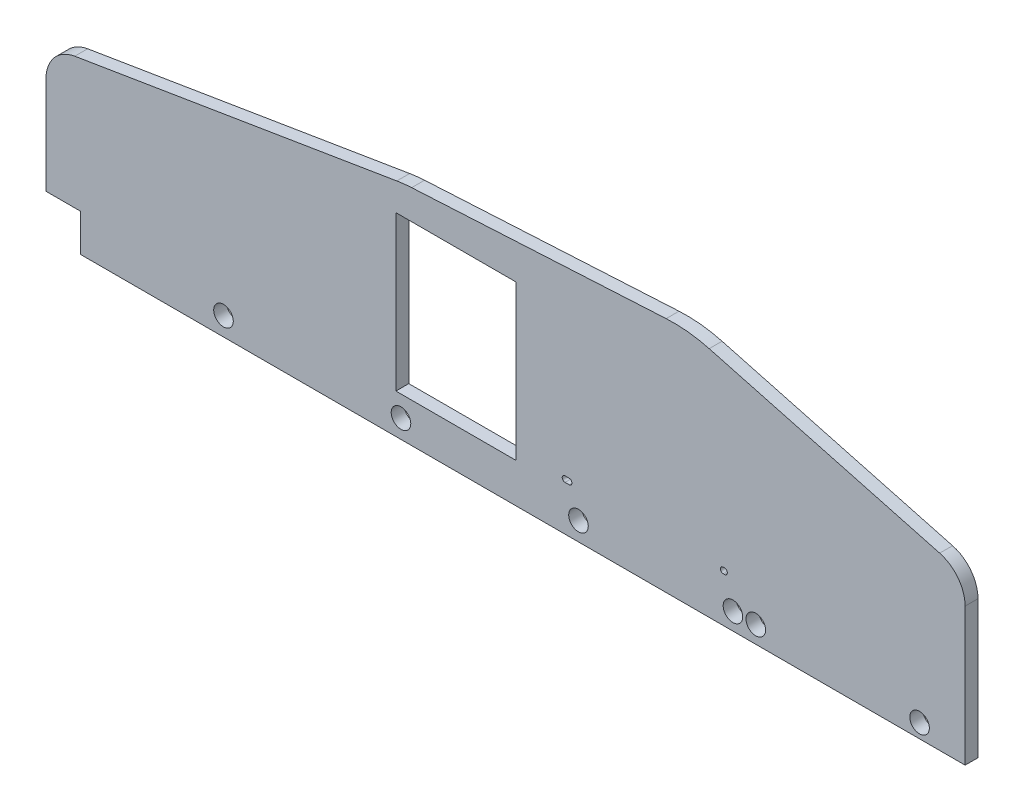
SolidWorks part; units mm, degrees
material "PC High Viscosity"
ref_plane "Front Plane" through (0, 0, 0) normal (0, 0, 1) x (1, 0, 0)
ref_plane "Top Plane" through (0, 0, 0) normal (0, 1, 0) x (1, 0, 0)
ref_plane "Right Plane" through (0, 0, 0) normal (1, 0, 0) x (0, 0, -1)
sketch "Sketch2" plane through (0, 0, 0) normal (0, 0, 1) x (1, 0, 0)
  line L0 (-340, 26.4) -> (-340, 121.4)
  line L1 (135, 176.4) -> (-75, 165)
  line L2 (135, 176.4) -> (340, 121.4)
  line L3 (340, 121.4) -> (340, 26.4)
  line L4 (340, 26.4) -> (340, 0)
  line L5 (-75, 165) -> (-340, 121.4)
  line L6 (340, 0) -> (-340, 0)
  line L7 (-340, 0) -> (-340, 26.4)
  circle A0 centre (-208.682, 13.7) radius 7.239
  circle A1 centre (-77.364, 13.7) radius 7.239
  circle A2 centre (53.954, 13.7) radius 7.239
  circle A3 centre (185.1267, 12.7) radius 7.239
  circle A4 centre (306.2847, 10.414) radius 7.239
  circle A5 centre (168.2251, 12.7) radius 7.239
  dimension "D7" = 14.478
  dimension "D11" = 12.7
  dimension "D1" = 165
  dimension "D2" = 680
  dimension "D3" = 95
  dimension "D4" = 475
  dimension "D5" = 150
  dimension "D6" = 210
  dimension "D8" = 95
  dimension "D9" = 26.4
  dimension "D12" = 10.414
extrude "Boss-Extrude1" add sketch "Sketch2" along normal mid plane 9.525
fillet "Fillet1" radius 25.4 2 edges at (340, 121.4, 0) (-340, 121.4, 0)
fillet "Fillet2" radius 101.6 2 edges at (-75, 165, 0) (135, 176.4, 0)
sketch "Sketch3" plane through (0, 0, 4.7625) normal (0, 0, 1) x (1, 0, 0)
  line L0 (0, 0) -> (0, 192.0016) construction
  line L1 (-340, 0) -> (-314.6, 0)
  line L2 (-340, 0) -> (-340, 27.686)
  line L3 (-340, 27.686) -> (-314.6, 27.686)
  line L4 (-314.6, 0) -> (-314.6, 27.686)
  line L5 (0, 192.0016) -> (0, -60.0751) construction
  dimension "D1" = 25.4
  dimension "D2" = 27.686
extrude "Cut-Extrude1" cut sketch "Sketch3" against normal through all
sketch "Sketch5" plane through (0, 0, 4.7625) normal (0, 0, 1) x (1, 0, 0)
  line L1 (-314.6, 0) -> (340, 0) construction
  line L3 (-81.1185, 29.1465) -> (7.7815, 29.1465)
  line L5 (7.7815, 29.1465) -> (7.7815, 143.4465)
  line L6 (7.7815, 143.4465) -> (-81.1185, 143.4465)
  line L7 (340, 0) -> (340, 101.9164) construction
  line L8 (-81.1185, 29.1465) -> (-81.1185, 143.4465)
  dimension "D2" = 29.1465
  dimension "D1" = 332.2185
  dimension "D3" = 114.3
  dimension "D4" = 88.9
extrude "Cut-Extrude2" cut sketch "Sketch5" against normal through all
sketch "Sketch8" plane through (0, 0, 4.7625) normal (0, 0, 1) x (1, 0, 0)
  line L0 (161, 35.3) -> (162, 35.3) construction
  line L1 (161, 37.4) -> (162, 37.4)
  line L2 (161, 33.2) -> (162, 33.2)
  line L3 (47, 35.3) -> (44, 35.3) construction
  line L4 (47, 33.2) -> (44, 33.2)
  line L5 (47, 37.4) -> (44, 37.4)
  line L6 (-314.6, 0) -> (340, 0) construction
  line L10 (-340, 99.8375) -> (-340, 27.686) construction
  arc A0 (161, 37.4) -> (161, 33.2) centre (161, 35.3) ccw
  arc A1 (162, 33.2) -> (162, 37.4) centre (162, 35.3) ccw
  arc A2 (47, 33.2) -> (47, 37.4) centre (47, 35.3) ccw
  arc A3 (44, 37.4) -> (44, 33.2) centre (44, 35.3) ccw
  point P2 (161.5, 35.3)
  point P9 (45.5, 35.3)
  dimension "D2" = 1
  dimension "D1" = 2.1
  dimension "D3" = 35.3
  dimension "D4" = 384
  dimension "D5" = 115.5
  dimension "D6" = 3
extrude "Cut-Extrude3" cut sketch "Sketch8" against normal through all
